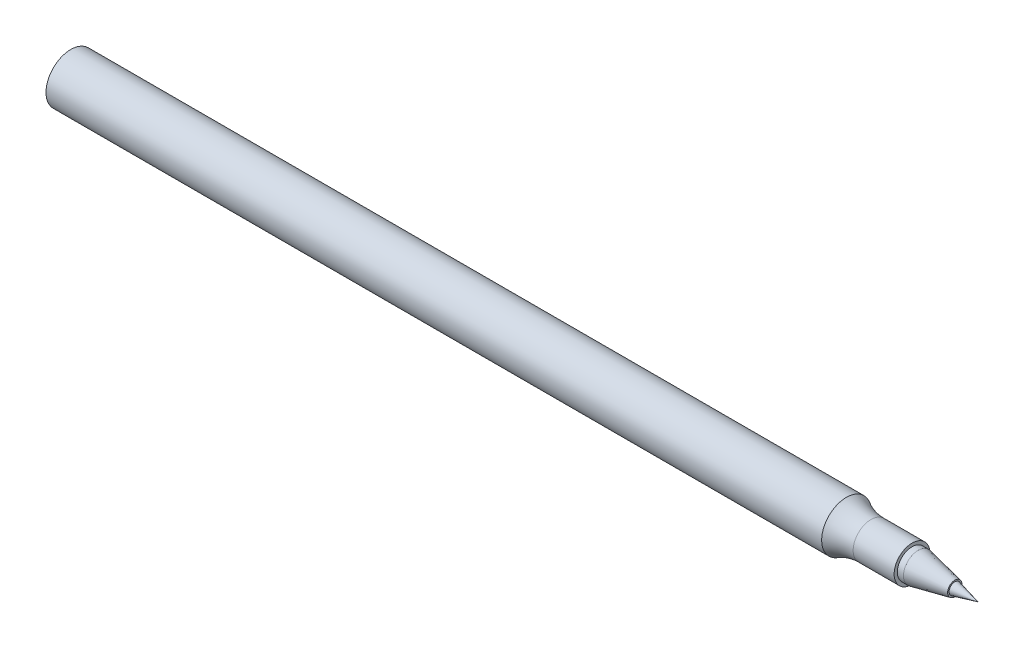
SolidWorks part; units mm, degrees
ref_plane "Front Plane" through (0, 0, 0) normal (0, 0, 1) x (1, 0, 0)
ref_plane "Top Plane" through (0, 0, 0) normal (0, 1, 0) x (1, 0, 0)
ref_plane "Right Plane" through (0, 0, 0) normal (1, 0, 0) x (0, 0, -1)
sketch "Sketch1" plane through (0, 0, 0) normal (0, 0, 1) x (1, 0, 0)
  line L0 (0, 0) -> (-85.9738, 0) construction
  line L1 (-85.9738, 0) -> (-85.9738, 3.9497)
  line L2 (-85.9738, 3.9497) -> (37.6988, 3.9497)
  line L3 (41.6297, 2.8575) -> (48.1636, 2.8575)
  line L4 (48.1636, 2.8575) -> (48.1636, 2.3495)
  line L5 (48.1636, 2.3495) -> (49.1429, 2.3495)
  line L6 (49.1429, 2.3495) -> (54.9848, 1.1459)
  line L7 (54.9848, 1.1459) -> (54.9848, 0.9144)
  line L8 (54.9848, 0.9144) -> (58.6792, 0)
  line L9 (0, 0) -> (58.6792, 0) construction
  line L10 (-85.9738, 0) -> (58.6792, 0)
  arc A0 (37.6988, 3.9497) -> (41.6297, 2.8575) centre (41.6297, 10.4775) ccw
  dimension "D7" = 7.62
  dimension "D1" = 144.653
  dimension "D2" = 7.8994
  dimension "D3" = 123.6726
  dimension "D4" = 10.4648
  dimension "D5" = 5.715
  dimension "D6" = 0.508
  dimension "D8" = 48.1636
  dimension "D9" = 5.8418
  dimension "D10" = 0.2316
  dimension "D11" = 3.6944
  dimension "D12" = 13.901
revolve "Revolve1" add sketch "Sketch1" angle 360 about L10
